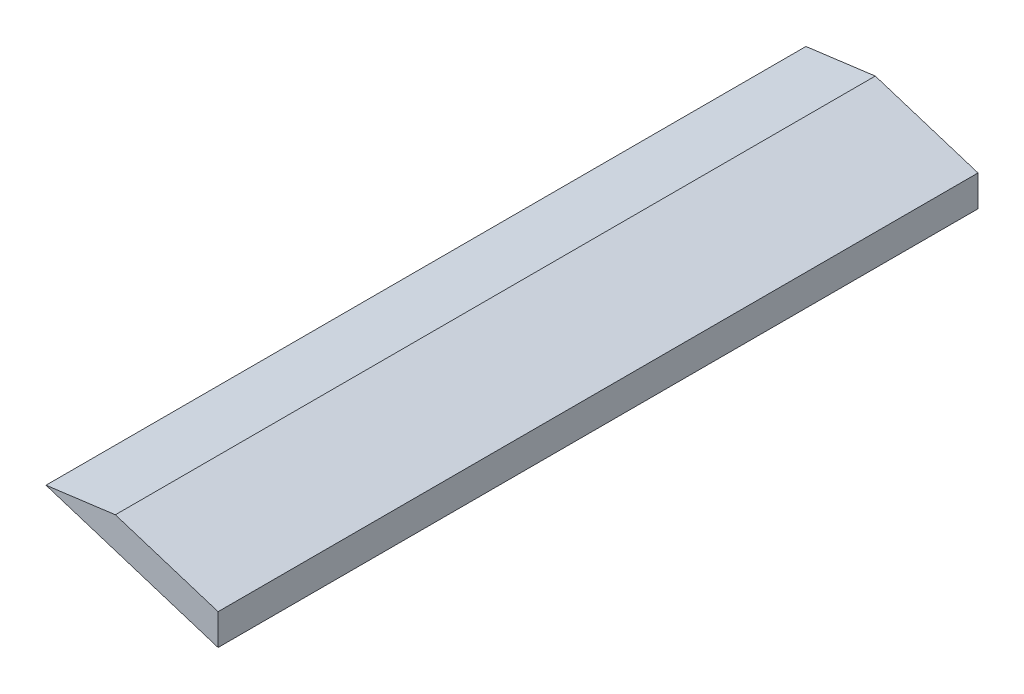
SolidWorks part; units mm, degrees
ref_plane "Front Plane" through (0, 0, 0) normal (0, 0, 1) x (1, 0, 0)
ref_plane "Top Plane" through (0, 0, 0) normal (0, 1, 0) x (1, 0, 0)
ref_plane "Right Plane" through (0, 0, 0) normal (1, 0, 0) x (0, 0, -1)
sketch "Sketch2" plane through (0, 0, 0) normal (0, 0, 1) x (1, 0, 0)
  line L0 (259.1, -276.9314) -> (259.1, -280.0785)
  line L1 (259.1, -276.9314) -> (248.6912, -273.633)
  line L2 (259.1, -280.0785) -> (241.6622, -274.5526)
  line L6 (241.6622, -274.5526) -> (248.6912, -273.633)
  line L9 (259.1, -287.9) -> (259.1, -280.3379) construction
  line L12 (259.1, -280.0785) -> (259.1, -276.9314) construction
  line L16 (-17.6214, -76.2979) -> (286.6296, -308.9357) construction
  line L17 (-14.5843, -72.3259) -> (289.6666, -304.9638) construction
  circle A1 centre (277.9804, -217.3514) radius 62.5 construction
  dimension "D1" = 3
extrude "Boss-Extrude1" add sketch "Sketch2" along normal up to surface (77 mm away)
